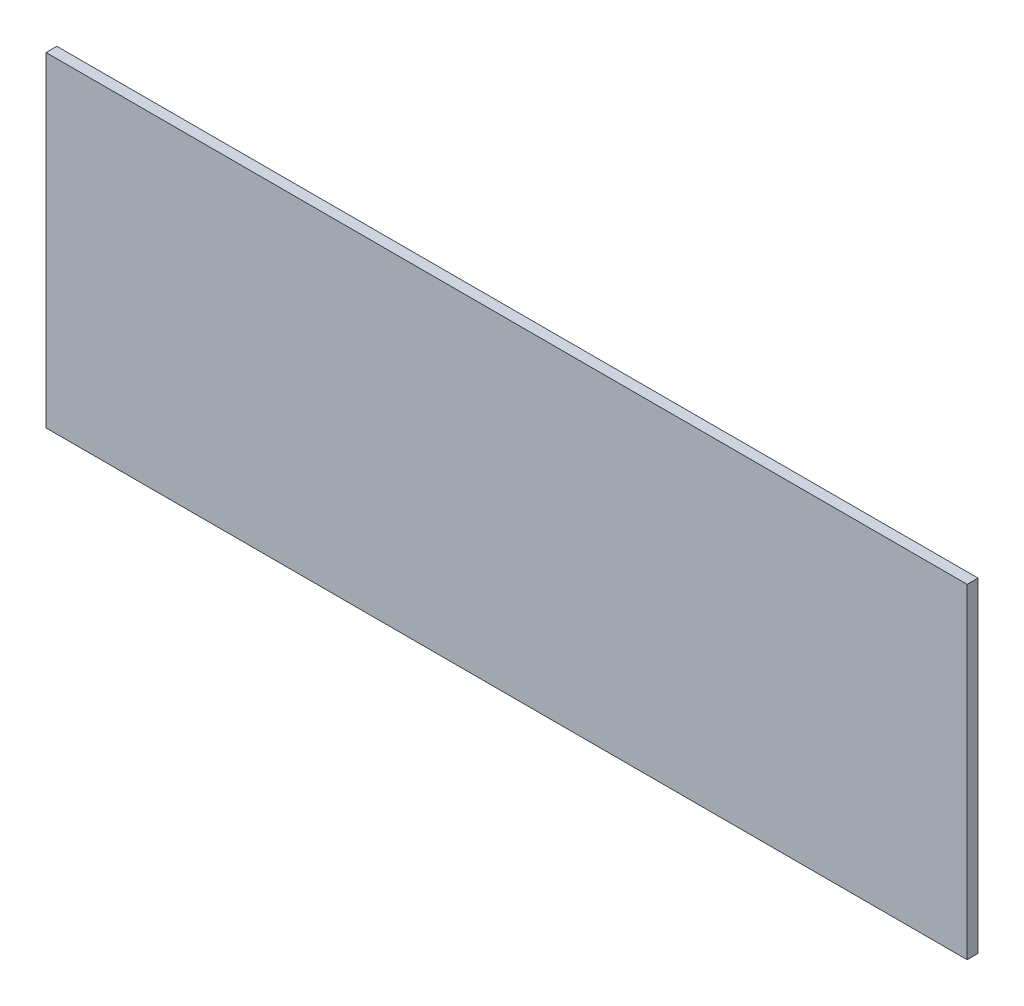
SolidWorks part; units mm, degrees
ref_plane "Спереди" through (0, 0, 0) normal (0, 0, 1) x (1, 0, 0)
ref_plane "Сверху" through (0, 0, 0) normal (0, 1, 0) x (1, 0, 0)
ref_plane "Справа" through (0, 0, 0) normal (1, 0, 0) x (0, 0, -1)
sketch "Эскиз1" plane through (0, 0, 0) normal (0, 0, 1) x (1, 0, 0)
  line L1 (425, -150) -> (-425, -150)
  line L2 (425, -150) -> (425, 150)
  line L3 (425, 150) -> (-425, 150)
  line L4 (-425, -150) -> (-425, 150)
  line L5 (425, -150) -> (-425, 150) construction
  line L6 (425, 150) -> (-425, -150) construction
  point P0 (0, 0)
  dimension "D1" = 300
  dimension "D2" = 850
extrude "Бобышка-Вытянуть1" add sketch "Эскиз1" along normal blind 10
